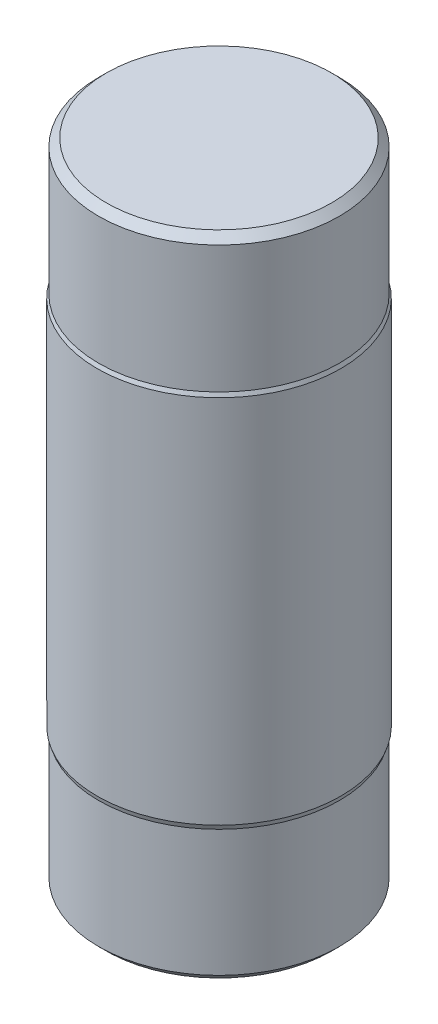
SolidWorks part; units mm, degrees
ref_plane "Front Plane" through (0, 0, 0) normal (0, 0, 1) x (1, 0, 0)
ref_plane "Top Plane" through (0, 0, 0) normal (0, 1, 0) x (1, 0, 0)
ref_plane "Right Plane" through (0, 0, 0) normal (1, 0, 0) x (0, 0, -1)
sketch "Sketch1" plane through (0, 0, 0) normal (0, 1, 0) x (1, 0, 0)
  circle A0 centre (0, 0) radius 3.95
  dimension "D1" = 7.9
extrude "Boss-Extrude1" add sketch "Sketch1" along normal mid plane 12 contours A0
sketch "Sketch2" plane through (0, 0, 0) normal (0, 0, 1) x (1, 0, 0)
  line L0 (-3.95, -6) -> (-3.95, 6)
  line L1 (3.95, 6) -> (3.95, -6)
  line L2 (3.95, 6) -> (3.95, -6)
  line L3 (-3.95, -6) -> (-3.95, 6)
  line L4 (0, -10.5) -> (0, 10.5) construction
  line L7 (-3.9, 6.125) -> (-3.95, 6)
  line L8 (3.9, 10.5) -> (3.9, 6.125)
  line L9 (3.9, 6.125) -> (3.95, 6)
  line L10 (-3.9, 6.125) -> (3.9, 6.125) construction
  line L11 (3.95, 6) -> (-3.95, 6) construction
  line L13 (-3.9, -10.5) -> (-3.9, -6.15)
  line L14 (-3.9, -6.15) -> (-3.95, -6)
  line L16 (3.9, -6.15) -> (3.95, -6)
  line L17 (-3.9, -6.15) -> (3.9, -6.15) construction
  line L18 (-3.95, -6) -> (3.95, -6) construction
  line L19 (0, 10.5) -> (0, 6)
  line L20 (0, -10.5) -> (0, -6)
  line L21 (0, 10.5) -> (3.9, 10.5)
  line L22 (-3.9, -10.5) -> (0, -10.5)
  line L23 (0, 6) -> (3.95, 6)
  line L24 (0, -6) -> (-3.95, -6)
  point P8 (0, 0)
  point P12 (0, 10.5)
  point P19 (0, -10.5)
  dimension "D1" = 21
  dimension "D2" = 3.9
  dimension "D3" = 0.125
  dimension "D4" = 3.9
  dimension "D5" = 0.15
  dimension "D6" = 3.9
  dimension "D7" = 3.9
revolve "Revolve2" add sketch "Sketch2" angle 360 about L4
chamfer "Chamfer1" distance 0.25 angle 45 2 edges at (3.9, -10.5, 0) (3.9, 10.5, 0)
